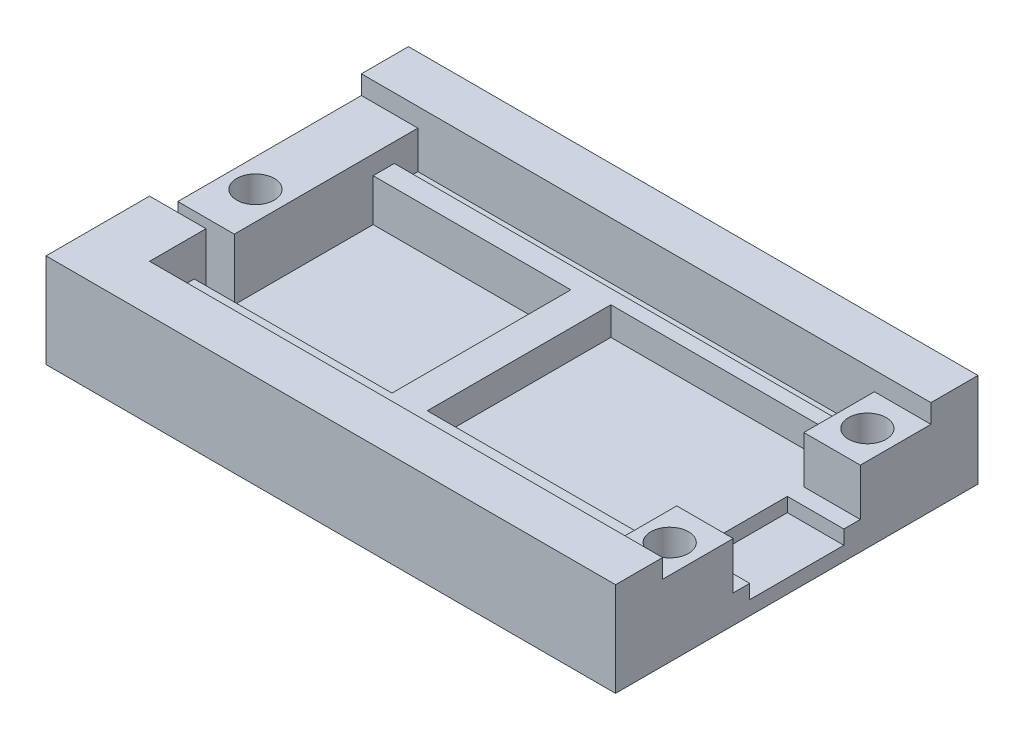
SolidWorks part; units mm, degrees
ref_plane "Front Plane" through (0, 0, 0) normal (0, 0, 1) x (1, 0, 0)
ref_plane "Top Plane" through (0, 0, 0) normal (0, 1, 0) x (1, 0, 0)
ref_plane "Right Plane" through (0, 0, 0) normal (1, 0, 0) x (0, 0, -1)
sketch "Sketch1" plane through (0, 0, 0) normal (0, 1, 0) x (1, 0, 0)
  line L1 (-24.0143, 18.9186) -> (36.4857, 18.9186)
  line L2 (-24.0143, 18.9186) -> (-24.0143, -19.5814)
  line L3 (-24.0143, -19.5814) -> (36.4857, -19.5814)
  line L4 (36.4857, 18.9186) -> (36.4857, -19.5814)
  dimension "D1" = 60.5
  dimension "D2" = 38.5
extrude "Boss-Extrude1" add sketch "Sketch1" along normal blind 6
sketch "Sketch2" plane through (0, 6, 0) normal (0, 1, 0) x (1, 0, 0)
  line L0 (36.4857, -19.5814) -> (36.4857, 18.9186) construction
  line L1 (-24.0143, -19.5814) -> (36.4857, -19.5814)
  line L2 (-24.0143, -19.5814) -> (-24.0143, -14.5814)
  line L3 (-18.0143, -14.5814) -> (30.4857, -14.5814)
  line L4 (36.4857, -19.5814) -> (36.4857, -14.5814)
  line L6 (-24.0143, 18.9186) -> (36.4857, 18.9186)
  line L7 (-24.0143, 18.9186) -> (-24.0143, 13.9186)
  line L8 (-24.0143, 13.9186) -> (30.4857, 13.9186)
  line L9 (36.4857, 18.9186) -> (36.4857, 13.9186)
  line L11 (-24.0143, -14.5814) -> (-24.0143, -8.5814)
  line L12 (-24.0143, -8.5814) -> (-18.0143, -8.5814)
  line L13 (-18.0143, -14.5814) -> (-18.0143, -8.5814)
  line L19 (36.4857, 13.9186) -> (36.4857, 6.4186)
  line L20 (36.4857, 6.4186) -> (30.4857, 6.4186)
  line L21 (30.4857, 13.9186) -> (30.4857, 6.4186)
  line L23 (36.4857, -14.5814) -> (36.4857, -7.0814)
  line L24 (36.4857, -7.0814) -> (30.4857, -7.0814)
  line L25 (30.4857, -14.5814) -> (30.4857, -7.0814)
  dimension "D1" = 5
  dimension "D2" = 5
  dimension "D3" = 6
  dimension "D4" = 6
  dimension "D5" = 7.5
  dimension "D6" = 7.5
  dimension "D7" = 6
  dimension "D8" = 6
extrude "Boss-Extrude2" add sketch "Sketch2" along normal blind 4
sketch "Sketch4" plane through (0, 6, 0) normal (0, 1, 0) x (1, 0, 0)
  line L0 (-18.0143, -8.5814) -> (-24.0143, -8.5814) construction
  line L1 (-24.0143, 13.9186) -> (-18.0143, 13.9186)
  line L2 (-24.0143, 13.9186) -> (-24.0143, -5.5814)
  line L3 (-24.0143, -5.5814) -> (-18.0143, -5.5814)
  line L4 (-18.0143, 13.9186) -> (-18.0143, -5.5814)
  dimension "D1" = 6
  dimension "D2" = 3
extrude "Boss-Extrude4" add sketch "Sketch4" along normal blind 2
sketch "Sketch6" plane through (0, 8, 0) normal (0, 1, 0) x (1, 0, 0)
  line L0 (-24.0143, 13.9186) -> (-24.0143, -5.5814) construction
  line L1 (-18.0143, 13.9186) -> (-24.0143, 13.9186) construction
  circle A0 centre (-21.0143, -0.3314) radius 2
  dimension "D1" = 3
  dimension "D2" = 14.25
extrude "Cut-Extrude1" cut sketch "Sketch6" against normal through all
sketch "Sketch7" plane through (0, 6, 0) normal (0, 1, 0) x (1, 0, 0)
  line L0 (30.4857, 13.9186) -> (30.4857, 6.4186) construction
  line L1 (-18.0143, 13.9186) -> (30.4857, 13.9186)
  line L2 (-18.0143, 13.9186) -> (-18.0143, 11.4186)
  line L3 (-18.0143, 11.4186) -> (30.4857, 11.4186)
  line L4 (30.4857, 13.9186) -> (30.4857, 11.4186)
  line L5 (30.4857, -7.0814) -> (30.4857, -14.5814) construction
  line L6 (-18.0143, -14.5814) -> (30.4857, -14.5814)
  line L7 (-18.0143, -14.5814) -> (-18.0143, -12.0814)
  line L8 (-18.0143, -12.0814) -> (30.4857, -12.0814)
  line L9 (30.4857, -14.5814) -> (30.4857, -12.0814)
  dimension "D1" = 2.5
  dimension "D2" = 2.5
extrude "Cut-Extrude2" cut sketch "Sketch7" against normal blind 2
sketch "Sketch8" plane through (0, 6, 0) normal (0, 1, 0) x (1, 0, 0)
  line L0 (-18.0143, -12.0814) -> (-18.0143, -8.5814) construction
  line L2 (-18.0143, -5.5814) -> (-18.0143, 9.1686)
  line L3 (-18.0143, 9.1686) -> (2.9857, 9.1686)
  line L4 (2.9857, -8.5814) -> (2.9857, 9.1686)
  line L5 (-18.0143, -5.5814) -> (-18.0143, 11.4186) construction
  line L6 (-24.0143, -5.5814) -> (-18.0143, -5.5814)
  line L7 (-24.0143, -5.5814) -> (-24.0143, -8.5814)
  line L8 (-24.0143, -8.5814) -> (-18.0143, -8.5814)
  line L14 (-18.0143, -8.5814) -> (-18.0143, -9.8314)
  line L15 (-18.0143, -9.8314) -> (2.9857, -9.8314)
  line L16 (2.9857, -8.5814) -> (2.9857, -9.8314)
  dimension "D1" = 17.75
  dimension "D2" = 21
  dimension "D3" = 1.25
extrude "Cut-Extrude3" cut sketch "Sketch8" against normal blind 4.5
sketch "Sketch9" plane through (0, 6, 0) normal (0, 1, 0) x (1, 0, 0)
  line L0 (30.4857, 11.4186) -> (30.4857, 6.4186) construction
  line L1 (30.4857, 9.9186) -> (6.4857, 9.9186)
  line L2 (30.4857, 9.9186) -> (30.4857, 6.4186)
  line L3 (30.4857, -9.5814) -> (6.4857, -9.5814)
  line L4 (6.4857, 9.9186) -> (6.4857, -9.5814)
  line L5 (30.4857, -12.0814) -> (-18.0143, -12.0814) construction
  line L7 (30.4857, -7.0814) -> (30.4857, -9.5814)
  line L8 (36.4857, 6.4186) -> (30.4857, 6.4186)
  line L9 (36.4857, 6.4186) -> (36.4857, -7.0814)
  line L10 (36.4857, -7.0814) -> (30.4857, -7.0814)
  dimension "D1" = 19.5
  dimension "D2" = 24
  dimension "D3" = 2.5
extrude "Cut-Extrude4" cut sketch "Sketch9" against normal blind 3
sketch "Sketch10" plane through (0, 10, 0) normal (0, 1, 0) x (1, 0, 0)
  line L1 (36.4857, 6.4186) -> (30.4857, 6.4186)
  line L2 (36.4857, 6.4186) -> (36.4857, 13.9186)
  line L3 (36.4857, 13.9186) -> (30.4857, 13.9186)
  line L4 (30.4857, 6.4186) -> (30.4857, 13.9186)
  line L5 (30.4857, -14.5814) -> (36.4857, -14.5814)
  line L6 (30.4857, -14.5814) -> (30.4857, -7.0814)
  line L7 (30.4857, -7.0814) -> (36.4857, -7.0814)
  line L8 (36.4857, -14.5814) -> (36.4857, -7.0814)
extrude "Cut-Extrude5" cut sketch "Sketch10" against normal blind 2
sketch "Sketch13" plane through (0, 3, 0) normal (0, 1, 0) x (1, 0, 0)
  line L0 (36.4857, -7.0814) -> (36.4857, 6.4186) construction
  line L1 (30.4857, -5.3314) -> (36.4857, -5.3314)
  line L2 (30.4857, -5.3314) -> (30.4857, 4.6686)
  line L3 (30.4857, 4.6686) -> (36.4857, 4.6686)
  line L4 (36.4857, -5.3314) -> (36.4857, 4.6686)
  line L5 (30.4857, -7.0814) -> (36.4857, -7.0814) construction
  dimension "D1" = 10
  dimension "D2" = 1.75
extrude "Cut-Extrude6" cut sketch "Sketch13" against normal blind 1.5
sketch "Sketch14" plane through (0, 8, 0) normal (0, 1, 0) x (1, 0, 0)
  line L1 (36.4857, -14.5814) -> (36.4857, -7.0814) construction
  line L2 (36.4857, 6.4186) -> (36.4857, 13.9186) construction
  line L4 (36.4857, -7.0814) -> (30.4857, -7.0814) construction
  line L5 (30.4857, 6.4186) -> (36.4857, 6.4186) construction
  circle A0 centre (33.4857, -10.8314) radius 2
  circle A1 centre (33.4857, 10.1686) radius 2
  dimension "D1" = 3
  dimension "D2" = 3
  dimension "D3" = 3.75
  dimension "D4" = 3.75
extrude "Cut-Extrude7" cut sketch "Sketch14" against normal up to next
